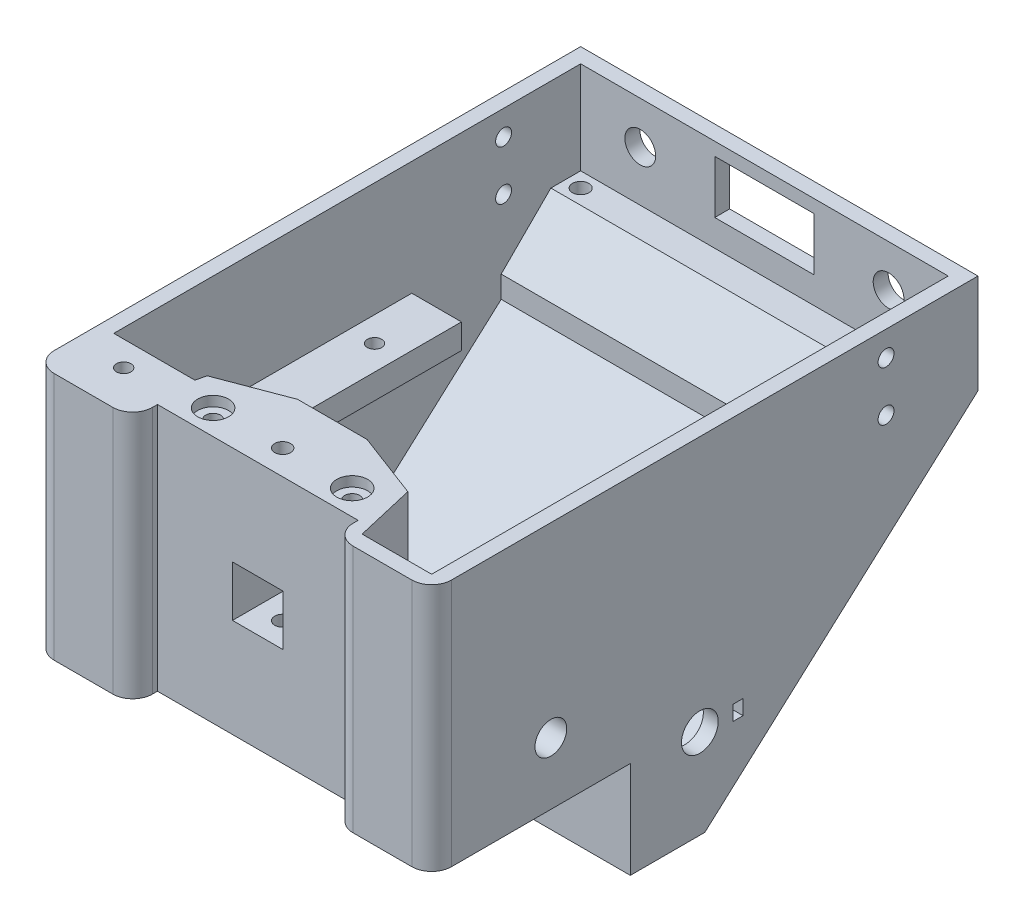
SolidWorks part; units mm, degrees
ref_plane "Спереди" through (0, 0, 0) normal (0, 0, 1) x (1, 0, 0)
ref_plane "Сверху" through (0, 0, 0) normal (0, 1, 0) x (1, 0, 0)
ref_plane "Справа" through (0, 0, 0) normal (1, 0, 0) x (0, 0, -1)
sketch "Sketch2" plane through (0, 0, 0) normal (1, 0, 0) x (0, 0, -1)
  line L0 (-27.3205, 20.9982) -> (-27.3205, -29.0018)
  line L1 (-27.3205, -29.0018) -> (12.6795, -29.0018)
  line L2 (12.6795, -29.0018) -> (12.6795, -48.5114)
  line L3 (12.6795, -48.5114) -> (27.6795, -48.5114)
  line L4 (82.6795, 20.9982) -> (82.6795, 0.9982)
  line L5 (82.6795, 20.9982) -> (-27.3205, 20.9982)
  line L6 (82.6795, 0.9982) -> (27.6795, -48.5114)
  dimension "D1" = 110
  dimension "D2" = 50
  dimension "D3" = 40
  dimension "D4" = 15
  dimension "D5" = 20
extrude "Boss-Extrude1" add sketch "Sketch2" along normal blind 80
shell "Shell1" thickness 3
sketch "Sketch3" plane through (0, 0, 24.3205) normal (0, 0, -1) x (-1, 0, 0)
  line L0 (-40, 20.9982) -> (-40, -26.0018) construction
  line L3 (-77, 20.9982) -> (-3, 20.9982) construction
  line L4 (-77, -26.0018) -> (-3, -26.0018) construction
  line L6 (-17, 20.9982) -> (-63, 20.9982)
  line L7 (-17, 20.9982) -> (-17, -26.0018)
  line L8 (-17, -26.0018) -> (-63, -26.0018)
  line L9 (-63, 20.9982) -> (-63, -26.0018)
  line L10 (-17, 20.9982) -> (-63, -26.0018) construction
  line L11 (-17, -26.0018) -> (-63, 20.9982) construction
  point P6 (-40, -2.5018)
  dimension "D1" = 46
extrude "Boss-Extrude2" add sketch "Sketch3" along normal blind 17
sketch "Sketch4" plane through (0, 0, 27.3205) normal (0, 0, 1) x (1, 0, 0)
  line L0 (0, 20.9982) -> (80, -29.0018) construction
  line L2 (45.1, -9.1018) -> (34.9, -9.1018)
  line L3 (45.1, -9.1018) -> (45.1, 1.0982)
  line L4 (45.1, 1.0982) -> (34.9, 1.0982)
  line L5 (34.9, -9.1018) -> (34.9, 1.0982)
  line L6 (45.1, -9.1018) -> (34.9, 1.0982) construction
  line L7 (45.1, 1.0982) -> (34.9, -9.1018) construction
  point P4 (40, -4.0018)
  dimension "D1" = 10.2
extrude "Cut-Extrude1" cut sketch "Sketch4" against normal up to surface (20 mm away) up to face at (40, -2.5018, 7.3205)
sketch "Sketch6" plane through (0, -29.0018, 0) normal (0, -1, 0) x (1, 0, 0)
  line L0 (40, 27.3205) -> (40, -12.6795) construction
  line L1 (47.5, -5.4795) -> (32.5, -5.4795)
  line L2 (47.5, -5.4795) -> (47.5, 7.3205)
  line L3 (47.5, 7.3205) -> (32.5, 7.3205)
  line L4 (32.5, -5.4795) -> (32.5, 7.3205)
  line L5 (47.5, -5.4795) -> (32.5, 7.3205) construction
  line L6 (47.5, 7.3205) -> (32.5, -5.4795) construction
  line L7 (80, -12.6795) -> (0, -12.6795) construction
  line L9 (80, 27.3205) -> (0, 27.3205) construction
  point P0 (40, 0.9205)
  dimension "D1" = 15
  dimension "D2" = 12.8
  dimension "D4" = 20
extrude "Cut-Extrude2" cut sketch "Sketch6" against normal up to surface (3 mm away) up to face at (40, -26.0018, 10.0705)
sketch "Sketch7" plane through (0, 0, 27.3205) normal (0, 0, 1) x (1, 0, 0)
  line L0 (40, 20.9982) -> (40, -29.0018) construction
  line L1 (80, 20.9982) -> (0, 20.9982) construction
  line L2 (80, -29.0018) -> (0, -29.0018) construction
  line L4 (60.2, -29.0018) -> (19.8, -29.0018)
  line L5 (60.2, -29.0018) -> (60.2, 20.9982)
  line L6 (60.2, 20.9982) -> (19.8, 20.9982)
  line L7 (19.8, -29.0018) -> (19.8, 20.9982)
  line L8 (60.2, -29.0018) -> (19.8, 20.9982) construction
  line L9 (60.2, 20.9982) -> (19.8, -29.0018) construction
  point P6 (40, -4.0018)
  dimension "D1" = 40.4
extrude "Cut-Extrude3" cut sketch "Sketch7" against normal blind 5
fillet "Fillet1" radius 4 4 edges at (19.8, -4.0018, 27.3205) (60.2, -4.0018, 27.3205) (80, -4.0018, 27.3205) (0, -4.0018, 27.3205)
sketch "Sketch12" plane through (0, 20.9982, 0) normal (0, 1, 0) x (1, 0, 0)
  line L0 (19.8, -22.3205) -> (19.8, -12.3205) construction
  line L1 (19.8, -12.3205) -> (60.2, -12.3205) construction
  line L2 (60.2, -12.3205) -> (60.2, -22.3205) construction
  line L3 (33, -7.3205) -> (19.8, -12.3205)
  line L4 (17, -7.3205) -> (63, -7.3205) construction
  line L5 (19.8, -12.3205) -> (17, -24.3205)
  line L6 (17, -24.3205) -> (17, -7.3205)
  line L7 (17, -7.3205) -> (33, -7.3205)
  line L8 (47, -7.3205) -> (63, -7.3205)
  line L9 (63, -7.3205) -> (63, -24.3205)
  line L10 (63, -24.3205) -> (60.2, -12.3205)
  line L11 (60.2, -12.3205) -> (47, -7.3205)
  dimension "D1" = 10
  dimension "D2" = 16
extrude "Cut-Extrude7" cut sketch "Sketch12" against normal up to surface (47 mm away) up to face at (40, -26.0018, 7.0205)
sketch "Sketch13" plane through (0, 20.9982, 0) normal (0, 1, 0) x (1, 0, 0)
  line L0 (19.8, -22.3205) -> (19.8, -12.3205) construction
  line L1 (19.8, -12.3205) -> (60.2, -12.3205) construction
  line L2 (60.2, -12.3205) -> (60.2, -22.3205) construction
  line L3 (60.2, -17.3205) -> (19.8, -17.3205) construction
  circle A0 centre (26, -17.3205) radius 1.5
  circle A1 centre (54, -17.3205) radius 1.5
  point P14 (40, -17.3205)
  dimension "D1" = 3
  dimension "D2" = 28
  dimension "D3" = 14
  dimension "D4" = 6.2
extrude "Cut-Extrude8" cut sketch "Sketch13" against normal blind 25
sketch "Sketch14" plane through (0, 20.9982, 0) normal (0, 1, 0) x (1, 0, 0)
  circle A0 centre (26, -17.3205) radius 3.1
  circle A1 centre (54, -17.3205) radius 3.1
  dimension "D1" = 6.2
extrude "Cut-Extrude9" cut sketch "Sketch14" against normal blind 2
sketch "Sketch17" plane through (77, 0, 0) normal (-1, 0, 0) x (0, 0, 1)
  line L0 (-45.6795, -2.0018) -> (-0.6795, -2.0018)
  line L1 (-0.6795, -2.0018) -> (-0.6795, -7.0018)
  line L2 (-0.6795, -7.0018) -> (-45.6795, -7.0018)
  line L3 (-45.6795, -7.0018) -> (-45.6795, -2.0018)
  line L4 (-79.6795, 20.9982) -> (24.3205, 20.9982) construction
  line L5 (-79.6795, 2.3342) -> (-79.6795, 20.9982) construction
  dimension "D1" = 45
  dimension "D2" = 5
  dimension "D3" = 23
  dimension "D4" = 34
extrude "Boss-Extrude5" add sketch "Sketch17" along normal up to surface (74 mm away) up to face at (3, -14.0994, -24.0865)
sketch "Sketch18" plane through (0, -2.0018, 0) normal (0, 1, 0) x (1, 0, 0)
  line L0 (40, 0.6795) -> (40, 45.6795) construction
  line L1 (3, 0.6795) -> (77, 0.6795) construction
  line L2 (3, 45.6795) -> (77, 45.6795) construction
  line L3 (77, 0.6795) -> (77, 45.6795) construction
  line L4 (13, 0.6795) -> (67, 0.6795)
  line L5 (13, 0.6795) -> (13, 45.6795)
  line L6 (13, 45.6795) -> (67, 45.6795)
  line L7 (67, 0.6795) -> (67, 45.6795)
  line L8 (13, 0.6795) -> (67, 45.6795) construction
  line L9 (13, 45.6795) -> (67, 0.6795) construction
  point P6 (40, 23.1795)
  dimension "D1" = 10
extrude "Cut-Extrude10" cut sketch "Sketch18" against normal up to next
sketch "Sketch19" plane through (0, -2.0018, 0) normal (0, 1, 0) x (1, 0, 0)
  line L0 (72, 45.6795) -> (72, 0.6795) construction
  line L1 (67, 45.6795) -> (77, 45.6795) construction
  line L2 (67, 0.6795) -> (77, 0.6795) construction
  line L3 (8, 45.6795) -> (8, 0.6795) construction
  line L4 (3, 45.6795) -> (13, 45.6795) construction
  line L5 (3, 0.6795) -> (13, 0.6795) construction
  circle A0 centre (72, 37.1795) radius 1.45
  circle A1 centre (72, 6.1795) radius 1.45
  circle A2 centre (8, 33.1795) radius 1.45
  circle A3 centre (8, 6.1795) radius 1.45
  point P20 (72, 23.1795)
  point P21 (8, 23.1795)
  dimension "D1" = 2.9
  dimension "D2" = 14
  dimension "D3" = 17
  dimension "D4" = 17
  dimension "D5" = 10
extrude "Cut-Extrude11" cut sketch "Sketch19" against normal up to next
sketch "Sketch21" plane through (0, -26.0018, 0) normal (0, 1, 0) x (1, 0, 0)
  line L0 (3, -24.3205) -> (3, -14.3205)
  line L1 (3, -24.3205) -> (3, 15.6795) construction
  line L2 (3, -14.3205) -> (19.3333, -14.3205)
  line L3 (19.8, -12.3205) -> (17, -24.3205) construction
  line L4 (19.3333, -14.3205) -> (17, -24.3205)
  line L6 (3, -24.3205) -> (17, -24.3205)
  dimension "D1" = 10
extrude "Boss-Extrude6" add sketch "Sketch21" along normal up to surface (47 mm away) up to face at (54, 20.9982, 20.4205)
sketch "Sketch22" plane through (0, 20.9982, 0) normal (0, 1, 0) x (1, 0, 0)
  line L0 (0, 82.6795) -> (0, -23.3205) construction
  line L1 (15.8, -27.3205) -> (4, -27.3205) construction
  circle A0 centre (10, -19.3205) radius 1.45
  dimension "D1" = 2.9
  dimension "D2" = 10
  dimension "D3" = 8
extrude "Cut-Extrude12" cut sketch "Sketch22" against normal through all
sketch "Sketch24" plane through (80, 0, 0) normal (1, 0, 0) x (0, 0, -1)
  line L0 (12.6795, -48.5114) -> (27.6795, -48.5114) construction
  line L1 (12.6795, -29.0018) -> (12.6795, -48.5114) construction
  line L2 (18.1795, -30.5114) -> (18.1795, -19.0114) construction
  line L3 (18.1795, -19.0114) -> (35.1795, -19.0114) construction
  line L4 (35.1795, -19.0114) -> (35.1795, -30.5114) construction
  line L5 (26.6795, -19.0114) -> (26.6795, -39.0114) construction
  line L6 (30.3795, -30.5114) -> (34.3795, -30.5114) construction
  line L8 (33.3795, -32.0114) -> (35.3795, -32.0114)
  line L9 (33.3795, -32.0114) -> (33.3795, -29.0114)
  line L10 (33.3795, -29.0114) -> (35.3795, -29.0114)
  line L11 (35.3795, -32.0114) -> (35.3795, -29.0114)
  line L12 (33.3795, -32.0114) -> (35.3795, -29.0114) construction
  line L13 (33.3795, -29.0114) -> (35.3795, -32.0114) construction
  circle A0 centre (26.6795, -30.5114) radius 3.7
  circle A1 centre (26.6795, -30.5114) radius 8.5 construction
  dimension "D1" = 7.4
  dimension "D2" = 17
  dimension "D3" = 18
  dimension "D4" = 14
  dimension "D5" = 20
  dimension "D6" = 4
  dimension "D7" = 2
  dimension "D8" = 3
extrude "Cut-Extrude13" cut sketch "Sketch24" against normal up to next
sketch "Sketch26" plane through (3, 0, 0) normal (1, 0, 0) x (0, 0, -1)
  line L0 (79.6795, 2.3342) -> (63.6795, 2.3342)
  line L1 (63.6795, 2.3342) -> (63.6795, -12.0686)
  line L2 (26.5281, -45.5114) -> (79.6795, 2.3342) construction
  line L3 (63.6795, -12.0686) -> (79.6795, 2.3342)
  dimension "D1" = 16
extrude "Boss-Extrude7" add sketch "Sketch26" along normal up to surface (74 mm away) up to face at (77, -30.5114, -34.3795)
sketch "Sketch27" plane through (0, 2.3342, 0) normal (0, 1, 0) x (1, 0, 0)
  line L0 (3, 76.6795) -> (77, 76.6795) construction
  line L1 (3, 79.6795) -> (3, 63.6795) construction
  line L2 (77, 79.6795) -> (77, 63.6795) construction
  line L3 (80, 82.6795) -> (0, 82.6795) construction
  circle A0 centre (6, 76.6795) radius 1.65
  circle A1 centre (74, 76.6795) radius 1.65
  point P10 (40, 76.6795)
  dimension "D1" = 3.3
  dimension "D2" = 68
  dimension "D3" = 34
  dimension "D4" = 6
extrude "Cut-Extrude14" cut sketch "Sketch27" against normal blind 10
sketch "Sketch28" plane through (0, 2.3342, 0) normal (0, 1, 0) x (1, 0, 0)
  line L1 (74, 79.9295) -> (71.1854, 78.3045)
  line L2 (71.1854, 78.3045) -> (71.1854, 75.0545)
  line L3 (71.1854, 75.0545) -> (74, 73.4295)
  line L4 (74, 73.4295) -> (76.8146, 75.0545)
  line L5 (76.8146, 75.0545) -> (76.8146, 78.3045)
  line L6 (76.8146, 78.3045) -> (74, 79.9295)
  line L7 (6, 73.4295) -> (8.8146, 75.0545)
  line L8 (8.8146, 75.0545) -> (8.8146, 78.3045)
  line L9 (8.8146, 78.3045) -> (6, 79.9295)
  line L10 (6, 79.9295) -> (3.1854, 78.3045)
  line L11 (3.1854, 78.3045) -> (3.1854, 75.0545)
  line L12 (3.1854, 75.0545) -> (6, 73.4295)
  circle A0 centre (74, 76.6795) radius 3.25 construction
  circle A1 centre (6, 76.6795) radius 3.25 construction
  dimension "D1" = 6.5
extrude "Cut-Extrude15" cut sketch "Sketch28" against normal blind 32 from offset 3 offset against normal yes
sketch "Sketch29" plane through (0, -29.0018, 0) normal (0, -1, 0) x (1, 0, 0)
  line L0 (0, 23.3205) -> (0, -12.6795) construction
  line L1 (7.1854, 17.6955) -> (10, 16.0705)
  line L2 (10, 16.0705) -> (12.8146, 17.6955)
  line L3 (12.8146, 17.6955) -> (12.8146, 20.9455)
  line L4 (12.8146, 20.9455) -> (10, 22.5705)
  line L5 (10, 22.5705) -> (7.1854, 20.9455)
  line L6 (7.1854, 20.9455) -> (7.1854, 17.6955)
  circle A0 centre (10, 19.3205) radius 3.25 construction
  dimension "D1" = 6.5
extrude "Cut-Extrude16" cut sketch "Sketch29" against normal blind 30
sketch "Sketch30" plane through (0, -26.0018, 0) normal (0, 1, 0) x (1, 0, 0)
  line L0 (77, -24.3205) -> (63, -24.3205)
  line L1 (63, -24.3205) -> (60.2, -12.3205)
  line L2 (63, -24.3205) -> (60.2, -12.3205) construction
  line L3 (60.2, -12.3205) -> (77, -12.3205)
  line L4 (77, -24.3205) -> (77, 15.6795) construction
  line L5 (77, -12.3205) -> (77, -24.3205)
  dimension "D1" = 12
extrude "Boss-Extrude8" add sketch "Sketch30" along normal blind 20
sketch "Sketch31" plane through (0, -6.0018, 0) normal (0, 1, 0) x (1, 0, 0)
  line L0 (76, -27.3205) -> (64.2, -27.3205) construction
  line L1 (80, -23.3205) -> (80, 12.6795) construction
  circle A0 centre (72, -21.3205) radius 1.5
  dimension "D3" = 3
  dimension "D1" = 6
  dimension "D2" = 8
extrude "Cut-Extrude17" cut sketch "Sketch31" against normal through all
sketch "Sketch32" plane through (0, -29.0018, 0) normal (0, -1, 0) x (1, 0, 0)
  line L1 (72, 24.5705) -> (69.1854, 22.9455)
  line L2 (69.1854, 22.9455) -> (69.1854, 19.6955)
  line L3 (69.1854, 19.6955) -> (72, 18.0705)
  line L4 (72, 18.0705) -> (74.8146, 19.6955)
  line L5 (74.8146, 19.6955) -> (74.8146, 22.9455)
  line L6 (74.8146, 22.9455) -> (72, 24.5705)
  circle A0 centre (72, 21.3205) radius 3.25 construction
  dimension "D1" = 6.5
extrude "Cut-Extrude18" cut sketch "Sketch32" against normal blind 15
sketch "Sketch33" plane through (0, -2.0018, 0) normal (0, 1, 0) x (1, 0, 0)
  line L0 (67, 40.6795) -> (77, 40.6795)
  line L1 (67, 0.6795) -> (67, 45.6795) construction
  line L2 (77, 0.6795) -> (77, 45.6795) construction
  line L3 (77, 40.6795) -> (77, 45.6795)
  line L4 (77, 45.6795) -> (67, 45.6795)
  line L5 (67, 45.6795) -> (67, 40.6795)
  dimension "D1" = 5
extrude "Cut-Extrude19" cut sketch "Sketch33" against normal up to next
sketch "Sketch34" plane through (0, 20.9982, 0) normal (0, 1, 0) x (1, 0, 0)
  line L0 (54, -17.3205) -> (26, -17.3205) construction
  circle A0 centre (40, -17.3205) radius 1.6
  dimension "D1" = 3.2
extrude "Cut-Extrude20" cut sketch "Sketch34" against normal through all
sketch "Sketch36" plane through (0, -29.0018, 0) normal (0, -1, 0) x (1, 0, 0)
  line L1 (38.375, 20.1351) -> (36.75, 17.3205)
  line L2 (36.75, 17.3205) -> (38.375, 14.5059)
  line L3 (38.375, 14.5059) -> (41.625, 14.5059)
  line L4 (41.625, 14.5059) -> (43.25, 17.3205)
  line L5 (43.25, 17.3205) -> (41.625, 20.1351)
  line L6 (41.625, 20.1351) -> (38.375, 20.1351)
  circle A0 centre (40, 17.3205) radius 3.25 construction
  dimension "D1" = 6.5
extrude "Cut-Extrude22" cut sketch "Sketch36" against normal blind 14
sketch "Sketch37" plane through (80, 0, 0) normal (1, 0, 0) x (0, 0, -1)
  line L0 (-23.3205, -16.5114) -> (63.2281, -16.5114) construction
  line L1 (-23.3205, 20.9982) -> (-23.3205, -29.0018) construction
  line L2 (27.6795, -48.5114) -> (82.6795, 0.9982) construction
  line L3 (30.3795, -30.5114) -> (22.9795, -30.5114) construction
  circle A0 centre (-3.3205, -16.5114) radius 3.2
  circle A1 centre (26.6795, -30.5114) radius 3.7 construction
  point P14 (26.6795, -30.5114)
  dimension "D1" = 6.4
  dimension "D2" = 14
  dimension "D3" = 20
extrude "Cut-Extrude23" cut sketch "Sketch37" against normal up to next
sketch "Sketch38" plane through (77, 0, 0) normal (-1, 0, 0) x (0, 0, 1)
  line L0 (12.3205, -26.0018) -> (-15.6795, -26.0018) construction
  line L1 (8.3205, -7.021) -> (-1.6795, -7.021)
  line L2 (8.3205, -7.021) -> (8.3205, -26.0018)
  line L3 (8.3205, -26.0018) -> (-1.6795, -26.0018)
  line L4 (-1.6795, -7.021) -> (-1.6795, -26.0018)
  line L5 (8.3205, -7.021) -> (-1.6795, -26.0018) construction
  line L6 (8.3205, -26.0018) -> (-1.6795, -7.021) construction
  circle A0 centre (3.3205, -16.5114) radius 3.2
  point P0 (3.3205, -16.5114)
  dimension "D1" = 10
extrude "Boss-Extrude9" add sketch "Sketch38" along normal blind 3
sketch "Sketch40" plane through (3, 0, 0) normal (1, 0, 0) x (0, 0, -1)
  line L0 (18.1795, -30.5114) -> (18.1795, -19.0114) construction
  line L1 (18.1795, -19.0114) -> (35.1795, -19.0114) construction
  line L2 (35.1795, -19.0114) -> (35.1795, -30.5114) construction
  line L3 (26.6795, -19.0114) -> (26.6795, -39.0114) construction
  line L4 (30.3795, -30.5114) -> (34.3795, -30.5114) construction
  line L5 (33.3795, -32.0114) -> (35.3795, -32.0114) construction
  line L6 (33.3795, -32.0114) -> (33.3795, -29.0114) construction
  line L7 (33.3795, -29.0114) -> (35.3795, -29.0114) construction
  line L8 (35.3795, -32.0114) -> (35.3795, -29.0114) construction
  line L9 (33.3795, -32.0114) -> (35.3795, -29.0114) construction
  line L10 (33.3795, -29.0114) -> (35.3795, -32.0114) construction
  line L13 (22.9795, -30.5114) -> (18.9795, -30.5114) construction
  line L14 (12.6795, -29.0018) -> (12.6795, -48.5114) construction
  line L15 (17.9795, -29.0114) -> (19.9795, -29.0114)
  line L16 (17.9795, -29.0114) -> (17.9795, -32.0114)
  line L17 (17.9795, -32.0114) -> (19.9795, -32.0114)
  line L18 (19.9795, -29.0114) -> (19.9795, -32.0114)
  line L19 (17.9795, -29.0114) -> (19.9795, -32.0114) construction
  line L20 (17.9795, -32.0114) -> (19.9795, -29.0114) construction
  line L21 (12.6795, -48.5114) -> (27.6795, -48.5114) construction
  circle A0 centre (26.6795, -30.5114) radius 3.7
  circle A1 centre (26.6795, -30.5114) radius 8.5 construction
  dimension "D4" = 17
  dimension "D5" = 17
  dimension "D11" = 7.4
  dimension "D1" = 3
  dimension "D2" = 2
  dimension "D3" = 4
  dimension "D6" = 2
  dimension "D7" = 3
  dimension "D8" = 4
  dimension "D9" = 14
  dimension "D10" = 18
extrude "Cut-Extrude24" cut sketch "Sketch40" against normal up to next
sketch "Sketch41" plane through (77, 0, 0) normal (-1, 0, 0) x (0, 0, 1)
  line L0 (-79.6795, 15.9982) -> (24.3205, 15.9982) construction
  line L1 (-79.6795, 2.3342) -> (-79.6795, 20.9982) construction
  line L2 (24.3205, 20.9982) -> (24.3205, -6.0018) construction
  line L3 (-79.6795, 20.9982) -> (24.3205, 20.9982) construction
  line L4 (-64.1622, 15.9982) -> (-64.1622, 5.9982) construction
  circle A0 centre (-64.1622, 15.9982) radius 1.6
  circle A1 centre (-64.1622, 5.9982) radius 1.6
  dimension "D1" = 3.2
  dimension "D4" = 10
  dimension "D2" = 15.5173
  dimension "D3" = 5
extrude "Cut-Extrude25" cut sketch "Sketch41" against normal through all both and the other way through all
sketch "Sketch43" plane through (0, 0, -79.6795) normal (0, 0, 1) x (1, 0, 0)
  line L0 (77, 13.0332) -> (3, 13.0332) construction
  line L1 (77, 2.3342) -> (77, 20.9982) construction
  line L2 (3, 2.3342) -> (3, 20.9982) construction
  line L3 (77, 20.9982) -> (3, 20.9982) construction
  line L4 (50, 7.6982) -> (30, 7.6982)
  line L5 (50, 7.6982) -> (50, 18.3682)
  line L6 (50, 18.3682) -> (30, 18.3682)
  line L7 (30, 7.6982) -> (30, 18.3682)
  line L8 (50, 7.6982) -> (30, 18.3682) construction
  line L9 (50, 18.3682) -> (30, 7.6982) construction
  circle A0 centre (15, 13.0332) radius 3.1 construction
  circle A1 centre (65, 13.0332) radius 3.1 construction
  point P6 (40, 13.0332)
  dimension "D4" = 6.2
  dimension "D5" = 50
  dimension "D1" = 20
  dimension "D2" = 10.67
  dimension "D3" = 2.63
  dimension "D6" = 25
extrude "Cut-Extrude26" cut sketch "Sketch43" against normal up to surface (3 mm away) up to face at (40, 10.9982, -82.6795)
chamfer "Chamfer1" distance 10 angle 45 1 edges at (40, 2.3342, -63.6795)
sketch "Sketch44" plane through (0, 0, -79.6795) normal (0, 0, 1) x (1, 0, 0)
  line L0 (77, 12.4682) -> (3, 12.4682) construction
  line L1 (77, 2.3342) -> (77, 20.9982) construction
  line L2 (3, 2.3342) -> (3, 20.9982) construction
  line L3 (77, 20.9982) -> (3, 20.9982) construction
  circle A0 centre (65, 12.4682) radius 3.1
  circle A1 centre (15, 12.4682) radius 3.1
  point P12 (40, 12.4682)
  dimension "D2" = 50
  dimension "D4" = 6.2
  dimension "D1" = 8.53
  dimension "D3" = 25
extrude "Cut-Extrude27" cut sketch "Sketch44" against normal through all
